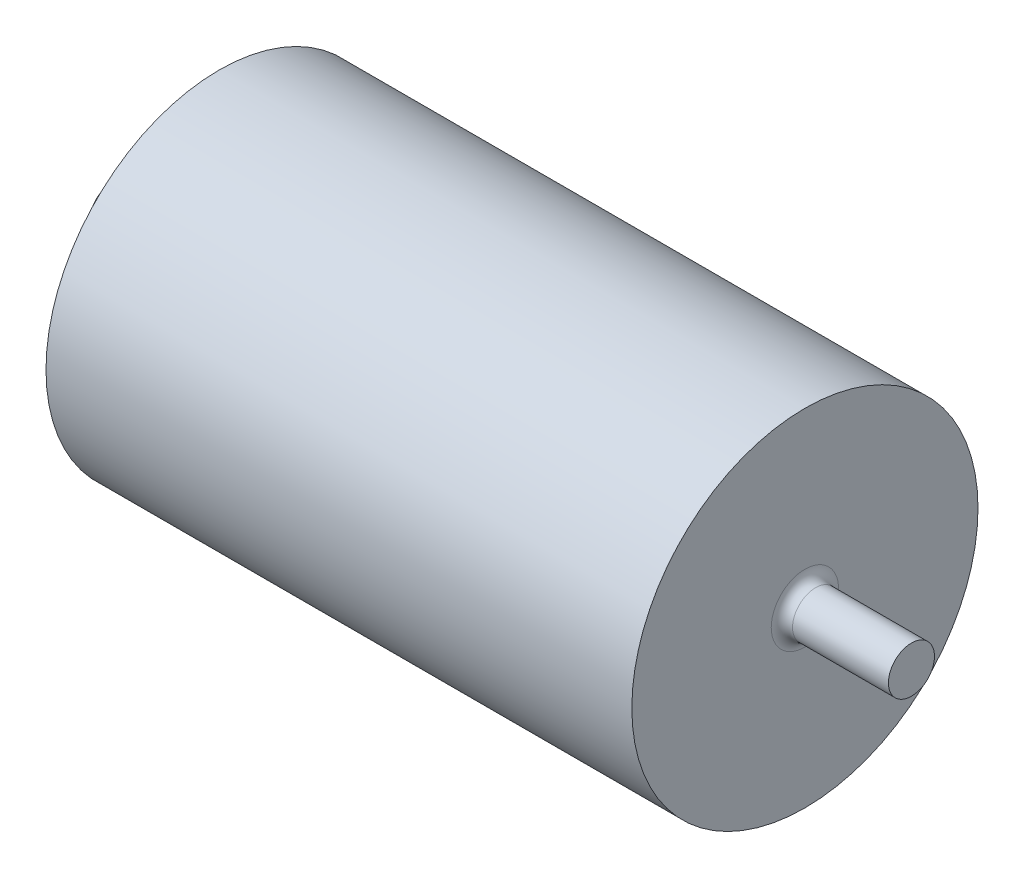
SolidWorks part; units mm, degrees
ref_plane "정면" through (0, 0, 0) normal (0, 0, 1) x (1, 0, 0)
ref_plane "윗면" through (0, 0, 0) normal (0, 1, 0) x (1, 0, 0)
ref_plane "우측면" through (0, 0, 0) normal (1, 0, 0) x (0, 0, -1)
sketch "스케치1" plane through (0, 0, 0) normal (0, 1, 0) x (1, 0, 0)
  line L0 (-130.1743, 0) -> (149.3432, 0) construction
  line L1 (0, 87.2185) -> (0, -90.7038) construction
  line L2 (55, 0) -> (-55, 0)
  line L4 (55, 0) -> (55, 32.5)
  line L5 (55, 32.5) -> (-55, 32.5)
  line L6 (-55, 0) -> (-55, 32.5)
  dimension "D1" = 32.5
  dimension "D2" = 110
  dimension "D3" = 55
revolve "회전1" add sketch "스케치1" angle 360 about L0
sketch "스케치2" plane through (55, 0, 0) normal (1, 0, 0) x (0, 0, -1)
  circle A0 centre (0, 0) radius 4.325
  dimension "D1" = 8.65
extrude "보스-돌출1" add sketch "스케치2" along normal blind 20
mirror "대칭 복사1" about plane through (0, 0, 0) normal (1, 0, 0) of "보스-돌출1"
fillet "필렛1" radius 2 2 edges at (-55, 0, -4.325) (55, 0, 4.325)
